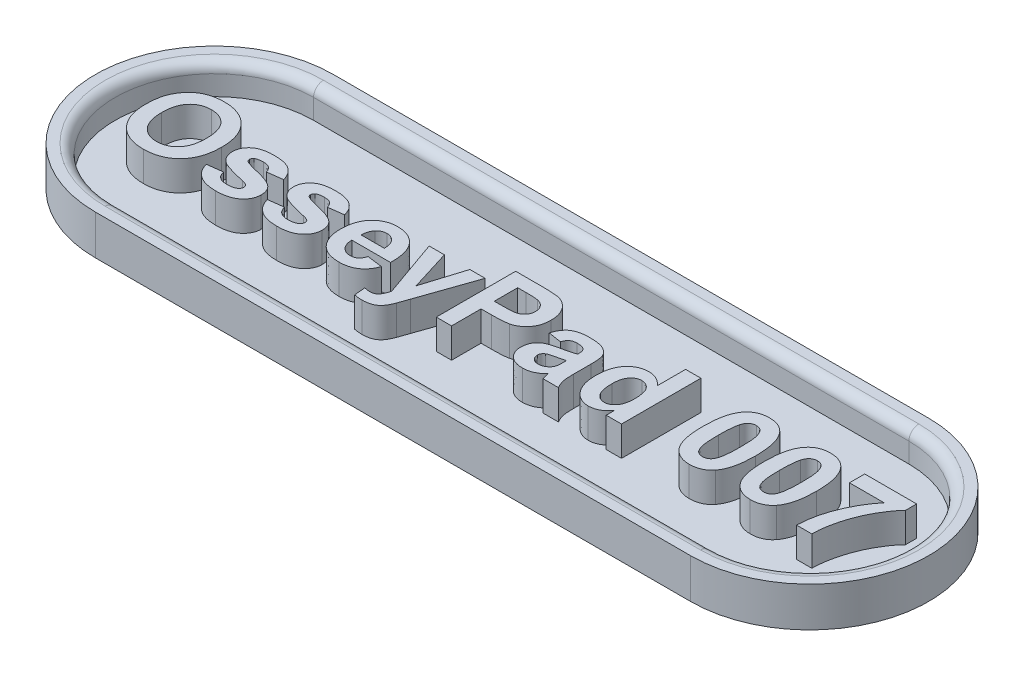
SolidWorks part; units mm, degrees
ref_plane "Front Plane" through (0, 0, 0) normal (0, 0, 1) x (1, 0, 0)
ref_plane "Top Plane" through (0, 0, 0) normal (0, 1, 0) x (1, 0, 0)
ref_plane "Right Plane" through (0, 0, 0) normal (1, 0, 0) x (0, 0, -1)
sketch "Sketch1" plane through (0, 0, 0) normal (0, 1, 0) x (1, 0, 0)
  line L0 (-15, 0) -> (15, 0) construction
  line L1 (-15, 6) -> (15, 6)
  line L2 (-15, -6) -> (15, -6)
  arc A0 (-15, 6) -> (-15, -6) centre (-15, 0) ccw
  arc A1 (15, -6) -> (15, 6) centre (15, 0) ccw
  point P2 (0, 0)
  dimension "D1" = 12
  dimension "D2" = 30
extrude "Boss-Extrude1" add sketch "Sketch1" along normal blind 2
sketch "Sketch2" plane through (0, 2, 0) normal (0, 1, 0) x (1, 0, 0)
  line L0 (-15, 0) -> (15, 0) construction
  line L1 (-15, 5) -> (15, 5)
  line L2 (-15, -5) -> (15, -5)
  arc A0 (-15, 5) -> (-15, -5) centre (-15, 0) ccw
  arc A1 (15, -5) -> (15, 5) centre (15, 0) ccw
  point P2 (0, 0)
  dimension "D1" = 30
  dimension "D2" = 10
extrude "Cut-Extrude1" cut sketch "Sketch2" against normal blind 1.5
sketch "Sketch3" plane through (0, 0.5, 0) normal (0, 1, 0) x (1, 0, 0)
  line L0 (-21, -1.995) -> (21, -1.995) construction
  line L1 (0, -8.7006) -> (0, 6.9821) construction
  line L3 (-15, -5) -> (15, -5) construction
  text T0 "OsseyPad 007" font "Arial" height 4
  dimension "D1" = 3.005
extrude "Boss-Extrude2" add sketch "Sketch3" along normal blind 1.5
fillet "Fillet1" radius 0.5 4 edges at (0, 2, -5) (20, 2, 0) (0, 2, 5) (-20, 2, 0)
